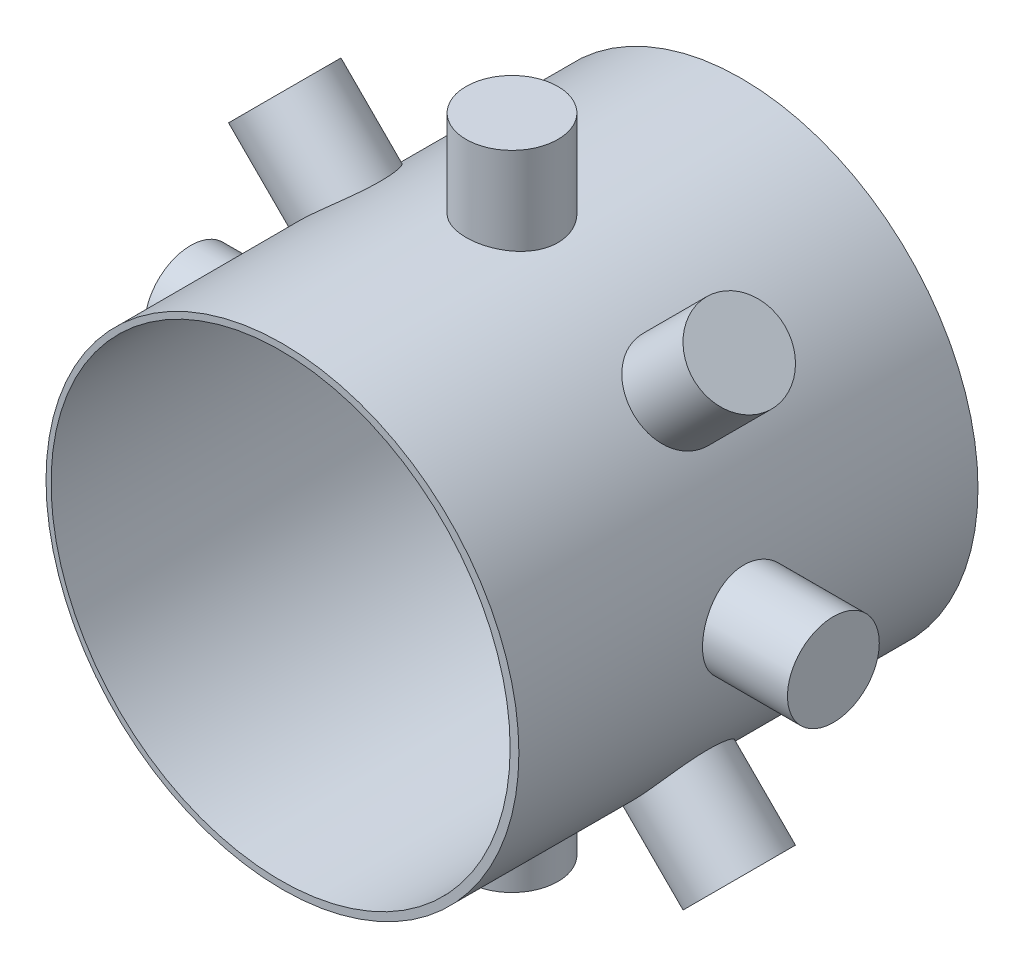
SolidWorks part; units mm, degrees
ref_plane "Front Plane" through (0, 0, 0) normal (0, 0, 1) x (1, 0, 0)
ref_plane "Top Plane" through (0, 0, 0) normal (0, 1, 0) x (1, 0, 0)
ref_plane "Right Plane" through (0, 0, 0) normal (1, 0, 0) x (0, 0, -1)
sketch "Sketch1" plane through (0, 0, 0) normal (0, 0, 1) x (1, 0, 0)
  line L0 (-0.4342, 0) -> (0.4537, 0) construction
  circle A0 centre (0, 0) radius 0.515
  circle A1 centre (-0.004, 0) radius 0.5
  dimension "D1" = 1.03
  dimension "D2" = 1
  dimension "D3" = 0.004
extrude "Boss-Extrude1" add sketch "Sketch1" along normal mid plane 1
ref_plane "Plane1" through (0.7, 0, 0) normal (1, 0, 0) x (0, 0, -1)
sketch "Sketch2" plane through (0.7, 0, 0) normal (1, 0, 0) x (0, 0, -1)
  line L0 (-0.3583, 0) -> (0.4195, 0) construction
  line L1 (0, 0.4471) -> (0, -0.4164) construction
  circle A0 centre (0, 0) radius 0.1
  dimension "D1" = 0.2
  dimension "D2" = 0
ref_axis "Axis1" through (0, 0, 0.5) along (0, 0, -1)
extrude "Boss-Extrude2" add sketch "Sketch2" against normal up to body
pattern_circular "CirPattern1" count 8 over 360 about axis through (0, 0, 0.5) along (0, 0, -1) of "Boss-Extrude2"
